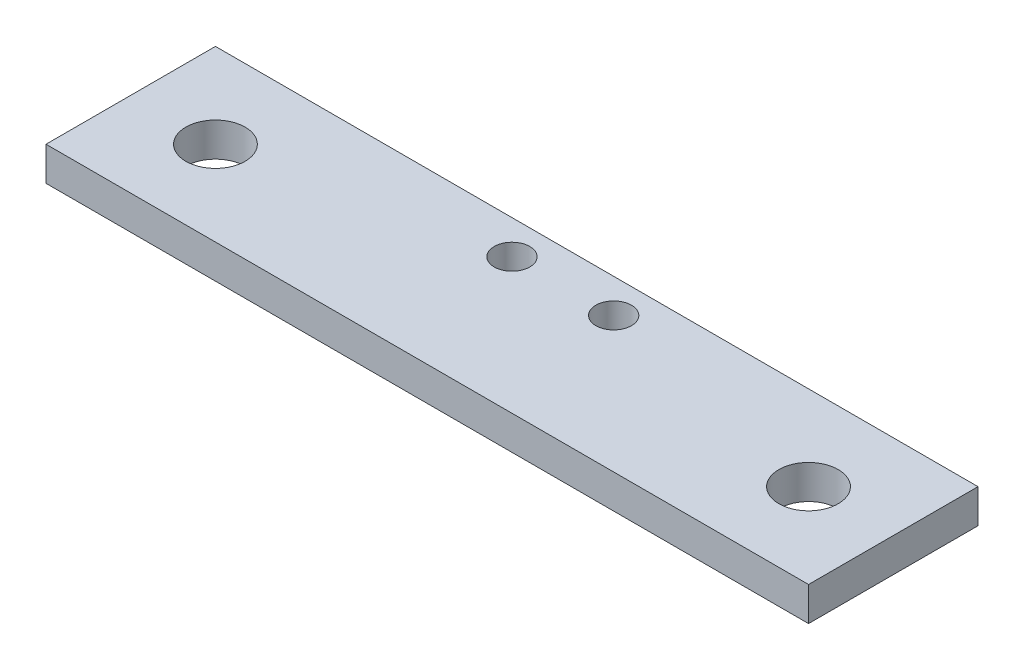
SolidWorks part; units mm, degrees
ref_plane "前视基准面" through (0, 0, 0) normal (0, 0, 1) x (1, 0, 0)
ref_plane "上视基准面" through (0, 0, 0) normal (0, 1, 0) x (1, 0, 0)
ref_plane "右视基准面" through (0, 0, 0) normal (1, 0, 0) x (0, 0, -1)
other "Configuration Table"
sketch "草图1" plane through (0, 0, 0) normal (0, 1, 0) x (1, 0, 0)
  line L1 (45, -10) -> (-45, -10)
  line L2 (45, -10) -> (45, 10)
  line L3 (45, 10) -> (-45, 10)
  line L4 (-45, -10) -> (-45, 10)
  line L5 (45, -10) -> (-45, 10) construction
  line L6 (45, 10) -> (-45, -10) construction
  point P0 (0, 0)
  dimension "D1" = 90
  dimension "D2" = 20
extrude "凸台-拉伸1" add sketch "草图1" along normal blind 4 contours L3 L4 L1 L2
sketch "草图2" plane through (0, 4, 0) normal (0, 1, 0) x (1, 0, 0)
  line L0 (45, 10) -> (-45, 10) construction
  circle A0 centre (-35, 0) radius 3.5
  circle A1 centre (35, 0) radius 3.5
  circle A2 centre (-6, 6) radius 2.1
  circle A3 centre (6, 6) radius 2.1
  point P11 (0, 0)
  dimension "D3" = 7
  dimension "D4" = 7
  dimension "D6" = 4.2
  dimension "D7" = 4.2
  dimension "D1" = 35
  dimension "D2" = 35
  dimension "D5" = 4
  dimension "D8" = 12
  dimension "D9" = 6
extrude "切除-拉伸1" cut sketch "草图2" against normal blind 10 contours A0 | A1 | A2 | A3
